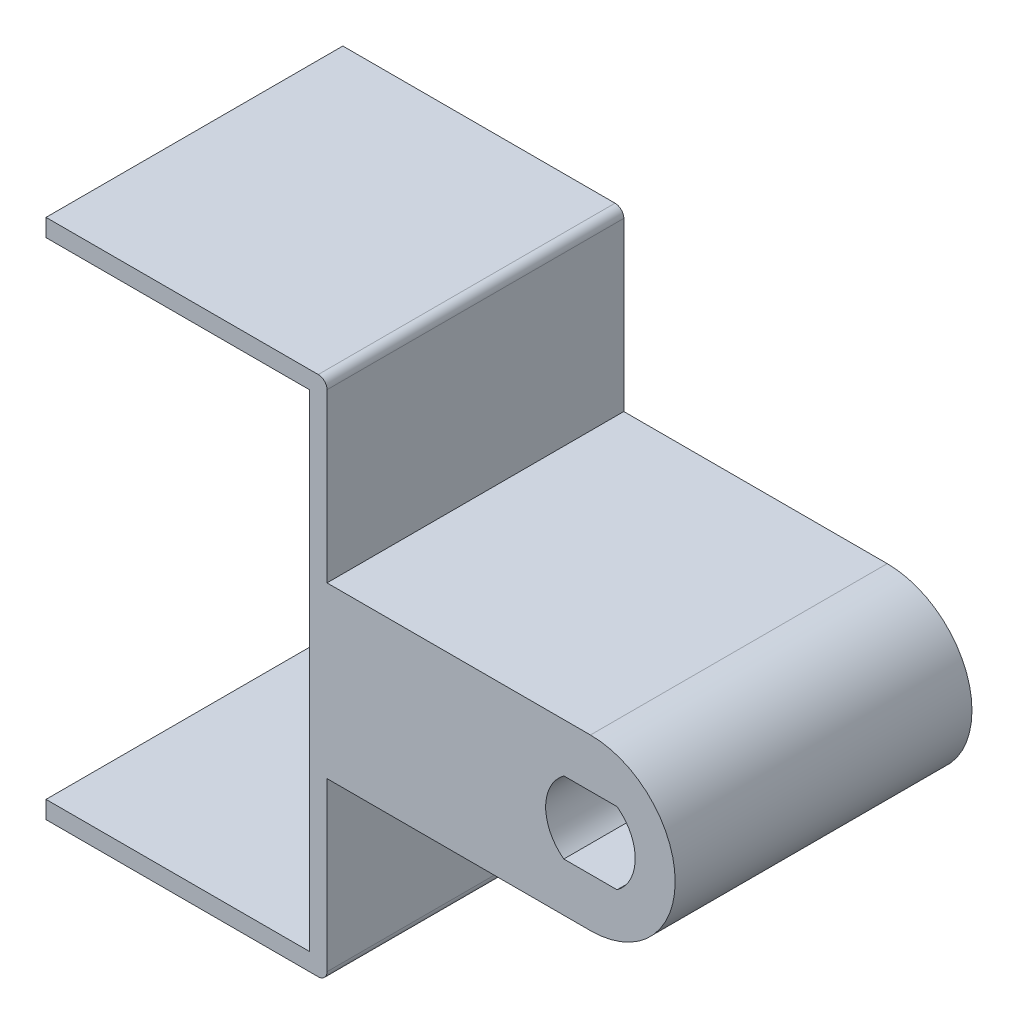
SolidWorks part; units mm, degrees
ref_plane "Front Plane" through (0, 0, 0) normal (0, 0, 1) x (1, 0, 0)
ref_plane "Top Plane" through (0, 0, 0) normal (0, 1, 0) x (1, 0, 0)
ref_plane "Right Plane" through (0, 0, 0) normal (1, 0, 0) x (0, 0, -1)
sketch "Sketch1" plane through (0, 0, 0) normal (0, 0, 1) x (1, 0, 0)
  line L0 (-20, -13.85) -> (20, -13.85)
  line L1 (20, -13.85) -> (20, 13.85)
  line L2 (20, 13.85) -> (-20, 13.85)
  line L3 (-20, -14.85) -> (21, -14.85)
  line L4 (21, -14.85) -> (21, 14.85)
  line L5 (21, 14.85) -> (-20, 14.85)
  line L6 (-20, 14.85) -> (-20, 13.85)
  line L7 (-20, -13.85) -> (-20, -14.85)
  point P8 (0, -13.85)
  point P9 (20, 0)
  dimension "D2" = 27.7
  dimension "D3" = 40
  dimension "D1" = 1
extrude "Boss-Extrude1" add sketch "Sketch1" along normal blind 16.9
sketch "Sketch4" plane through (0, 0, 0) normal (0, 0, -1) x (-1, 0, 0)
  line L0 (-21, 4.825) -> (-36, 4.825)
  line L1 (-21, -14.85) -> (-21, 14.85) construction
  line L3 (-40.391, 2) -> (-30.875, 2)
  line L4 (-30.875, 2) -> (-30.875, -2)
  line L5 (-30.875, -2) -> (-40.391, -2)
  line L7 (-36, -4.825) -> (-21, -4.825)
  line L8 (-21, -4.825) -> (-21, 4.825)
  line L9 (-20, 13.85) -> (-20, -13.85) construction
  arc A0 (-36, -4.825) -> (-40.391, -2) centre (-36, 0) cw
  arc A1 (-36, 4.825) -> (-40.391, 2) centre (-36, 0) ccw
  circle A2 centre (-36, 0) radius 4.825 construction
  point P11 (-30.875, 0)
  point P14 (-21, 0)
  dimension "D3" = 4.825
  dimension "D1" = 4
  dimension "D2" = 9.65
  dimension "D4" = 0.3
  dimension "D5" = 16
extrude "Boss-Extrude2" add sketch "Sketch4" against normal blind 13.5
sketch "Sketch5" plane through (0, 0, 13.5) normal (0, 0, 1) x (1, 0, 0)
  line L6 (21, 4.825) -> (21, -4.825)
  line L7 (21, -4.825) -> (36, -4.825)
  line L8 (40.391, -2) -> (30.875, -2)
  line L9 (30.875, -2) -> (30.875, 2)
  line L10 (30.875, 2) -> (40.391, 2)
  line L11 (36, 4.825) -> (21, 4.825)
  line L12 (21, 4.825) -> (21, -4.825)
  line L13 (21, -4.825) -> (36, -4.825)
  line L17 (36, 4.825) -> (21, 4.825)
  arc A1 (40.391, 2) -> (40.391, -2) centre (36, 0) cw
  arc A2 (36, -4.825) -> (40.391, -2) centre (36, 0) ccw
  arc A3 (40.391, 2) -> (36, 4.825) centre (36, 0) ccw
  arc A4 (36, -4.825) -> (40.391, -2) centre (36, 0) ccw
  arc A5 (40.391, 2) -> (36, 4.825) centre (36, 0) ccw
  dimension "D1" = 0
extrude "Boss-Extrude3" add sketch "Sketch5" along normal up to surface (3.4 mm away) up to face at (0.25, 0, 16.9)
sketch "Sketch8" plane through (0, 0, 0) normal (0, 0, -1) x (-1, 0, 0)
  line L5 (-37.5, 2) -> (-40.391, 2)
  line L6 (-40.391, -2) -> (-37.5, -2)
  line L7 (-34.5, 2) -> (-30.875, 2)
  line L8 (-30.875, 2) -> (-30.875, -2)
  line L9 (-30.875, -2) -> (-34.5, -2)
  arc A2 (-34.5, -2) -> (-34.5, 2) centre (-36, 0) ccw
  arc A3 (-37.5, 2) -> (-37.5, -2) centre (-36, 0) ccw
  arc A4 (-40.391, 2) -> (-40.391, -2) centre (-36, 0) ccw
  dimension "D1" = 2.5
  dimension "D2" = 36
extrude "Boss-Extrude4" add sketch "Sketch8" against normal up to surface (13.5 mm away) up to face at (35.7415, 0, 13.5)
sketch "Sketch9" plane through (0, 0, 13.5) normal (0, 0, -1) x (-1, 0, 0)
  line L2 (-37.5, -2) -> (-34.5, -2)
  line L3 (-34.5, 2) -> (-37.5, 2)
  line L4 (-37.5, -2) -> (-34.5, -2)
  line L5 (-34.5, 2) -> (-37.5, 2)
  arc A1 (-34.5, -2) -> (-34.5, 2) centre (-36, 0) ccw
  arc A6 (-34.5, -2) -> (-34.5, 2) centre (-36, 0) ccw
  arc A7 (-37.5, 2) -> (-37.5, -2) centre (-36, 0) ccw
  arc A8 (-37.5, 2) -> (-37.5, -2) centre (-36, 0) ccw
  dimension "D1" = 0
extrude "Cut-Extrude1" cut sketch "Sketch9" against normal through all
chamfer "Chamfer1" distance 2 angle 30 4 edges at (33.5, 0, 0) (38.5, 0, 0) (36, -2, 0) (36, 2, 0)
sketch "Sketch10" plane through (0, 0, 0) normal (0, 0, -1) x (-1, 0, 0)
  line L0 (20, -14.85) -> (-21, -14.85) construction
  line L1 (20, 14.85) -> (-5, 14.85)
  line L2 (20, 14.85) -> (20, -14.85)
  line L3 (20, -14.85) -> (-5, -14.85)
  line L4 (-5, 14.85) -> (-5, -14.85)
  line L5 (-20, 13.85) -> (-20, -13.85) construction
  dimension "D1" = 15
sketch "Sketch11" plane through (0, 0, 0) normal (0, 0, -1) x (-1, 0, 0)
  line L0 (-37.5, -2) -> (-34.5, -2) construction
  line L1 (-34.5, 2) -> (-37.5, 2) construction
  line L2 (-37.5, -2) -> (-34.5, -2) construction
  line L3 (-34.5, 2) -> (-37.5, 2) construction
  line L4 (-34.4834, 2.05) -> (-37.5166, 2.05)
  line L5 (-37.5166, -2.05) -> (-34.4834, -2.05)
  arc A0 (-34.5, -2) -> (-34.5, 2) centre (-36, 0) ccw construction
  arc A1 (-37.5, 2) -> (-37.5, -2) centre (-36, 0) ccw construction
  arc A2 (-34.5, -2) -> (-34.5, 2) centre (-36, 0) ccw construction
  arc A3 (-37.5, 2) -> (-37.5, -2) centre (-36, 0) ccw construction
  arc A4 (-37.5166, 2.05) -> (-37.5166, -2.05) centre (-36, 0) ccw
  arc A5 (-34.4834, -2.05) -> (-34.4834, 2.05) centre (-36, 0) ccw
  dimension "D1" = 0.05
extrude "Cut-Extrude2" cut sketch "Sketch11" against normal through all
fillet "Fillet1" radius 0.5 4 edges at (-20, 14.85, 8.45) (-20, -14.85, 8.45) (21, 14.85, 8.45) (21, -14.85, 8.45)
sketch "Sketch6" plane through (0, 0, 16.9) normal (0, 0, 1) x (1, 0, 0)
  arc A0 (36, -4.825) -> (36, 4.825) centre (36, 0) ccw construction
  arc A1 (36, -4.825) -> (36, 4.825) centre (36, 0) ccw
  circle A2 centre (36, 0) radius 4.8263
extrude "Cut-Extrude3" cut sketch "Sketch10" against normal through all
